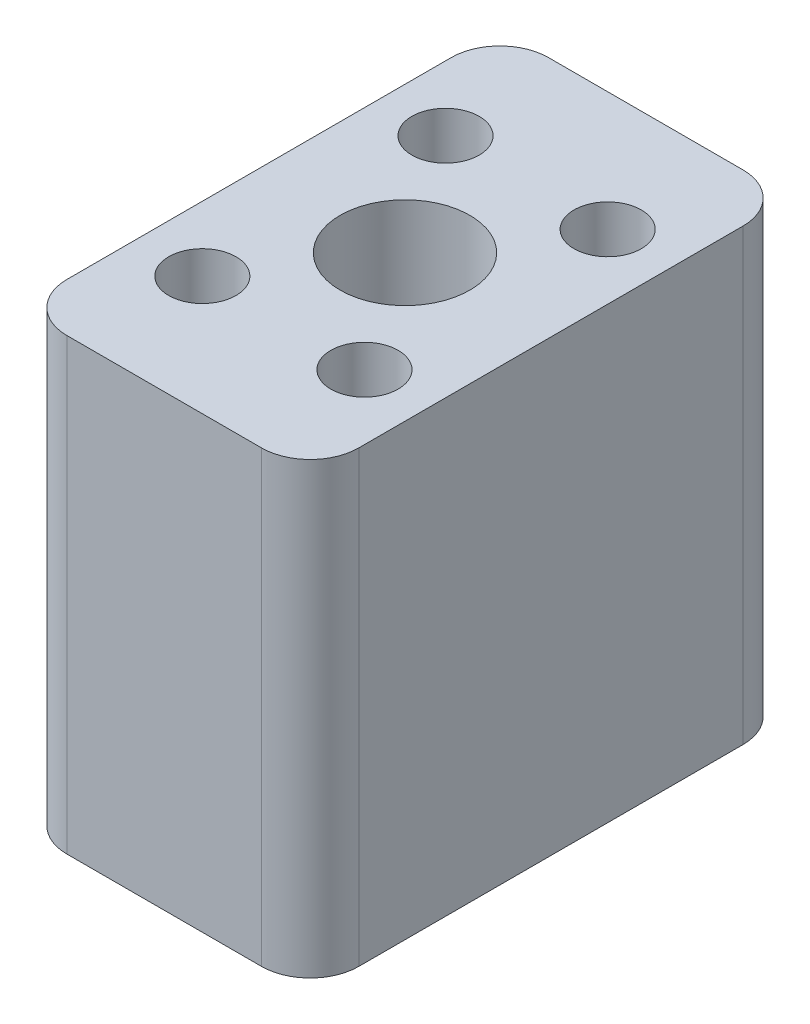
SolidWorks part; units mm, degrees
ref_plane "前视基准面" through (0, 0, 0) normal (0, 0, 1) x (1, 0, 0)
ref_plane "上视基准面" through (0, 0, 0) normal (0, 1, 0) x (1, 0, 0)
ref_plane "右视基准面" through (0, 0, 0) normal (1, 0, 0) x (0, 0, -1)
other "Configuration Table"
sketch "草图1" plane through (0, 0, 0) normal (0, 1, 0) x (1, 0, 0)
  line L1 (-9, -14.85) -> (9, -14.85)
  line L2 (-9, -14.85) -> (-9, 14.85)
  line L3 (-9, 14.85) -> (9, 14.85)
  line L4 (9, -14.85) -> (9, 14.85)
  line L5 (-9, -14.85) -> (9, 14.85) construction
  line L6 (-9, 14.85) -> (9, -14.85) construction
  point P0 (0, 0)
  dimension "D1" = 18
  dimension "D2" = 29.7
extrude "凸台-拉伸1" add sketch "草图1" along normal blind 27.7
sketch "草图2" plane through (0, 27.7, 0) normal (0, 1, 0) x (1, 0, 0)
  line L1 (-5, -7.5) -> (5, -7.5) construction
  line L2 (-5, -7.5) -> (-5, 7.5) construction
  line L3 (-5, 7.5) -> (5, 7.5) construction
  line L4 (5, -7.5) -> (5, 7.5) construction
  line L5 (-5, -7.5) -> (5, 7.5) construction
  line L6 (-5, 7.5) -> (5, -7.5) construction
  circle A0 centre (5, 7.5) radius 2.075
  circle A1 centre (-5, 7.5) radius 2.075
  circle A2 centre (-5, -7.5) radius 2.075
  circle A3 centre (5, -7.5) radius 2.075
  point P0 (0, 0)
  dimension "D1" = 4.15
  dimension "D2" = 10
  dimension "D3" = 15
extrude "切除-拉伸1" cut sketch "草图2" against normal blind 27.7
fillet "圆角1" radius 3 4 edges at (9, 13.85, 14.85) (-9, 13.85, 14.85) (-9, 13.85, -14.85) (9, 13.85, -14.85)
sketch "草图3" plane through (0, 27.7, 0) normal (0, 1, 0) x (1, 0, 0)
  circle A0 centre (0, 0) radius 4
  dimension "D1" = 8
extrude "切除-拉伸2" cut sketch "草图3" against normal blind 27.7
